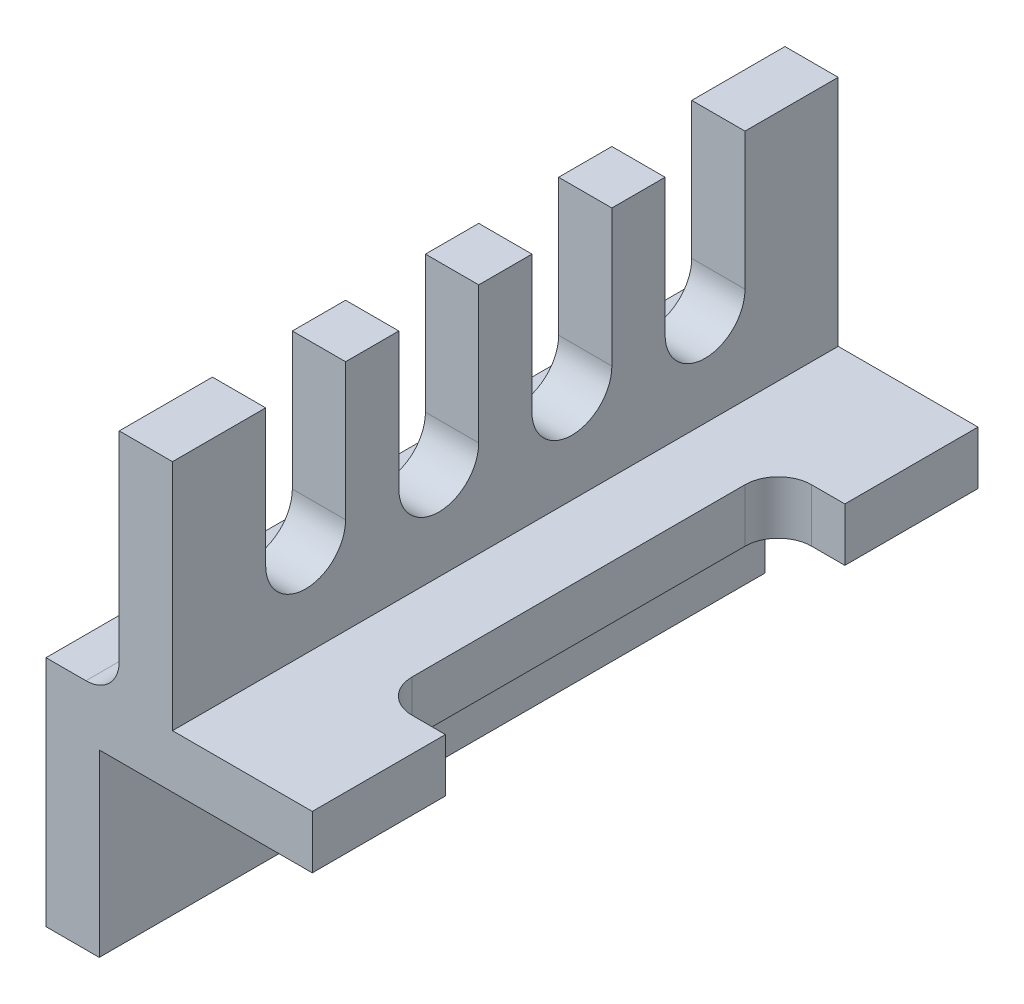
SolidWorks part; units mm, degrees
ref_plane "Front Plane" through (0, 0, 0) normal (0, 0, 1) x (1, 0, 0)
ref_plane "Top Plane" through (0, 0, 0) normal (0, 1, 0) x (1, 0, 0)
ref_plane "Right Plane" through (0, 0, 0) normal (1, 0, 0) x (0, 0, -1)
sketch "Sketch2" plane through (0, 0, 0) normal (0, 0, 1) x (1, 0, 0)
  line L0 (0, 0) -> (0, -35)
  line L1 (0, -35) -> (8, -35)
  line L2 (8, -35) -> (8, -8)
  line L3 (8, -8) -> (40, -8)
  line L4 (40, -8) -> (40, 0)
  line L5 (40, 0) -> (19, 0)
  line L6 (19, 0) -> (19, 35)
  line L7 (19, 35) -> (11, 35)
  line L8 (11, 35) -> (11, 0)
  line L9 (11, 0) -> (0, 0)
  dimension "D1" = 35
  dimension "D2" = 8
  dimension "D3" = 8
  dimension "D4" = 40
  dimension "D5" = 70
  dimension "D6" = 8
  dimension "D7" = 21
extrude "Boss-Extrude1" add sketch "Sketch2" along normal blind 100
sketch "Sketch3" plane through (0, 0, 0) normal (0, 1, 0) x (1, 0, 0)
  line L0 (40, -80) -> (30, -80)
  line L1 (40, -100) -> (40, 0) construction
  line L2 (30, -80) -> (30, -20)
  line L3 (30, -20) -> (40, -20)
  line L4 (40, -100) -> (19, -100) construction
  line L5 (40, -80) -> (40, -20)
  dimension "D1" = 10
  dimension "D2" = 60
  dimension "D3" = 20
extrude "Cut-Extrude1" cut sketch "Sketch3" against normal up to surface (8 mm away) up to face at (24, -8, 50)
sketch "Sketch4" plane through (19, 0, 0) normal (1, 0, 0) x (0, 0, -1)
  line L0 (-86, 35) -> (-86, 14.4402)
  line L1 (-100, 35) -> (0, 35) construction
  line L2 (-74, 35) -> (-74, 14.4402)
  line L3 (-100, 0) -> (-100, 35) construction
  line L4 (-86, 35) -> (-74, 35)
  arc A0 (-74, 14.4402) -> (-86, 14.4402) centre (-80, 14.4402) cw
  dimension "D1" = 20
  dimension "D2" = 12
extrude "Cut-Extrude2" cut sketch "Sketch4" against normal up to surface (8 mm away) up to face at (11, 17.5, 50)
pattern_linear "LPattern1" count 4 spacing 20 along (0, 0, -1) of "Cut-Extrude2"
fillet "Fillet1" radius 5 3 edges at (30, -4, 80) (30, -4, 20) (11, 0, 50)
